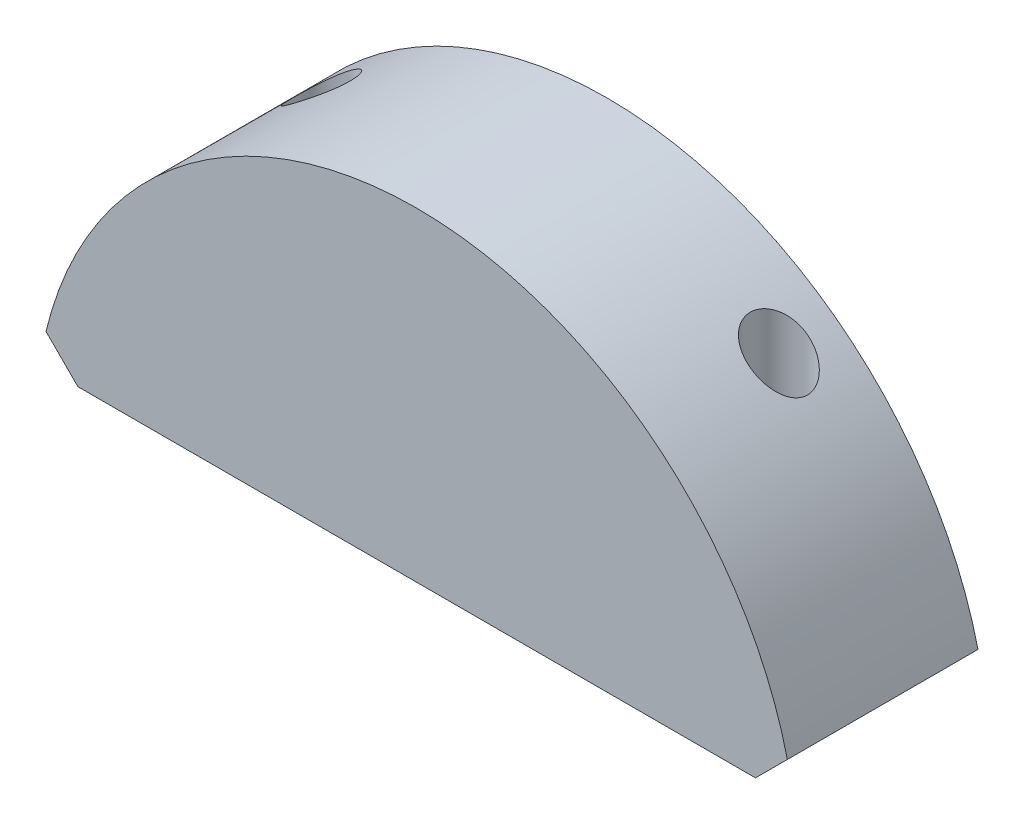
SolidWorks part; units mm, degrees
ref_plane "Plan de face" through (0, 0, 0) normal (0, 0, 1) x (1, 0, 0)
ref_plane "Plan de dessus" through (0, 0, 0) normal (0, 1, 0) x (1, 0, 0)
ref_plane "Plan de droite" through (0, 0, 0) normal (1, 0, 0) x (0, 0, -1)
sketch "Esquisse1" plane through (0, 0, 0) normal (0, 0, 1) x (1, 0, 0)
  line L0 (0, 0) -> (0, 9.1872) construction
  line L1 (17.7737, 3) -> (-17.7737, 3)
  line L2 (19.4465, 4.6728) -> (17.7737, 3)
  line L4 (-19.4465, 4.6728) -> (-17.7737, 3)
  arc A0 (19.4465, 4.6728) -> (-19.4465, 4.6728) centre (0, 0) ccw
  dimension "D1" = 35.5474
  dimension "D2" = 20
  dimension "D3" = 3
  dimension "D4" = 2.3656
extrude "Extrusion1" add sketch "Esquisse1" along normal blind 10
sketch "Esquisse2" plane through (0, 3, 0) normal (0, -1, 0) x (1, 0, 0)
  line L0 (0, 0) -> (0, 3) construction
  line L1 (-17.7737, 0) -> (17.7737, 0) construction
  line L2 (0, 3) -> (-12, 3) construction
  circle A0 centre (-12, 3) radius 1.5
  circle A1 centre (12, 3) radius 1.5
  dimension "D1" = 3
  dimension "D2" = 12
  dimension "D3" = 3
extrude "Extrusion2" cut sketch "Esquisse2" against normal through all
